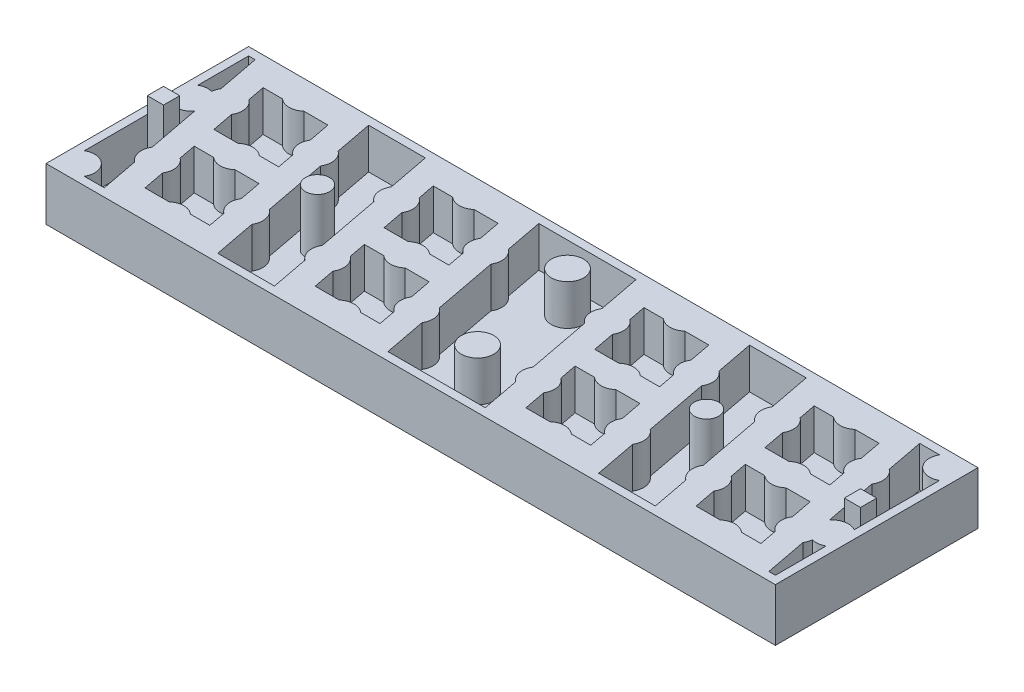
SolidWorks part; units mm, degrees
ref_plane "Спереди" through (0, 0, 0) normal (0, 0, 1) x (1, 0, 0)
ref_plane "Сверху" through (0, 0, 0) normal (0, 1, 0) x (1, 0, 0)
ref_plane "Сбоку" through (0, 0, 0) normal (1, 0, 0) x (0, 0, -1)
sketch "Эскиз1" plane through (0, 0, 0) normal (0, 1, 0) x (1, 0, 0)
  line L1 (0, 0) -> (90, 0)
  line L2 (0, 0) -> (0, 25)
  line L3 (0, 25) -> (90, 25)
  line L4 (90, 0) -> (90, 25)
  dimension "D1" = 90
  dimension "D2" = 25
extrude "Бобышка-Вытянуть1" add sketch "Эскиз1" along normal blind 1.5
sketch "Эскиз3" plane through (0, 1.5, 0) normal (0, 1, 0) x (1, 0, 0)
  line L0 (0, 25) -> (9, 25) construction
  line L1 (90, 25) -> (0, 25) construction
  line L2 (9, 25) -> (30, 25) construction
  line L3 (30, 25) -> (56, 25) construction
  line L4 (56, 25) -> (77, 25) construction
  line L5 (41.1905, 1) -> (53.1905, 1)
  line L6 (37.7143, 3.5) -> (35.3229, 3.5)
  line L7 (20.1905, 1) -> (27.1905, 1)
  line L8 (15.8095, 24) -> (22.8095, 24)
  line L9 (36.8095, 24) -> (48.8095, 24)
  line L10 (58.6771, 3.5) -> (55.7143, 3.5)
  line L11 (23.7995, 18.8027) -> (22.8095, 24)
  line L12 (35.7143, 14) -> (35.3056, 16.1459)
  line L13 (27.1905, 1) -> (26.3056, 5.6459)
  line L14 (2.7995, 18.8027) -> (1.8095, 24)
  line L15 (14.7143, 14) -> (14.3056, 16.1459)
  line L16 (6.1905, 1) -> (5.3056, 5.6459)
  line L17 (4.7995, 8.3027) -> (3.5695, 14.7603)
  line L18 (13.7995, 18.8027) -> (13.2857, 21.5)
  line L19 (20.1905, 1) -> (19.2005, 6.1973)
  line L20 (18.6944, 8.8541) -> (17.2005, 16.6973)
  line L21 (16.6944, 19.3541) -> (15.8095, 24)
  line L22 (25.7995, 8.3027) -> (24.3056, 16.1459)
  line L23 (8.7143, 3.5) -> (8.2005, 6.1973)
  line L24 (7.6944, 8.8541) -> (7.2857, 11)
  line L25 (34.7995, 18.8027) -> (34.2857, 21.5)
  line L26 (16.7143, 3.5) -> (16.3056, 5.6459)
  line L27 (15.7995, 8.3027) -> (15.2857, 11)
  line L28 (15.2857, 11) -> (12.3229, 11)
  line L29 (7.6771, 21.5) -> (5.2857, 21.5)
  line L30 (10.3229, 21.5) -> (13.2857, 21.5)
  line L31 (5.2857, 21.5) -> (5.6944, 19.3541)
  line L32 (14.7143, 14) -> (12.3229, 14)
  line L33 (1, 24) -> (1.8095, 24)
  line L34 (16.7143, 3.5) -> (14.3229, 3.5)
  line L35 (1, 24) -> (1, 17.7321)
  line L36 (3.7321, 1) -> (6.1905, 1)
  line L37 (89, 21.2679) -> (89, 10.7321)
  line L38 (9.6771, 11) -> (7.2857, 11)
  line L39 (9.6771, 14) -> (6.7143, 14)
  line L40 (6.7143, 14) -> (6.2005, 16.6973)
  line L41 (41.1905, 1) -> (40.2005, 6.1973)
  line L42 (39.6944, 8.8541) -> (38.2005, 16.6973)
  line L43 (37.6944, 19.3541) -> (36.8095, 24)
  line L44 (29.7143, 3.5) -> (29.2005, 6.1973)
  line L45 (28.6944, 8.8541) -> (28.2857, 11)
  line L46 (37.7143, 3.5) -> (37.3056, 5.6459)
  line L47 (36.7995, 8.3027) -> (36.2857, 11)
  line L48 (36.2857, 11) -> (33.3229, 11)
  line L49 (28.6771, 21.5) -> (26.2857, 21.5)
  line L50 (31.3229, 21.5) -> (34.2857, 21.5)
  line L51 (26.2857, 21.5) -> (26.6944, 19.3541)
  line L52 (35.7143, 14) -> (33.3229, 14)
  line L53 (63.7143, 3.5) -> (61.3229, 3.5)
  line L54 (30.6771, 11) -> (28.2857, 11)
  line L55 (30.6771, 14) -> (27.7143, 14)
  line L56 (27.7143, 14) -> (27.2005, 16.6973)
  line L57 (62.8095, 24) -> (69.8095, 24)
  line L59 (49.7995, 18.8027) -> (48.8095, 24)
  line L60 (61.7143, 14) -> (61.3056, 16.1459)
  line L61 (53.1905, 1) -> (52.3056, 5.6459)
  line L62 (51.7995, 8.3027) -> (50.3056, 16.1459)
  line L63 (60.7995, 18.8027) -> (60.2857, 21.5)
  line L64 (67.1905, 1) -> (66.2005, 6.1973)
  line L65 (65.6944, 8.8541) -> (64.2005, 16.6973)
  line L66 (63.6944, 19.3541) -> (62.8095, 24)
  line L67 (55.7143, 3.5) -> (55.2005, 6.1973)
  line L68 (54.6944, 8.8541) -> (54.2857, 11)
  line L69 (63.7143, 3.5) -> (63.3056, 5.6459)
  line L70 (62.7995, 8.3027) -> (62.2857, 11)
  line L71 (62.2857, 11) -> (59.3229, 11)
  line L72 (54.6771, 21.5) -> (52.2857, 21.5)
  line L73 (57.3229, 21.5) -> (60.2857, 21.5)
  line L74 (52.2857, 21.5) -> (52.6944, 19.3541)
  line L75 (61.7143, 14) -> (59.3229, 14)
  line L76 (79.6771, 3.5) -> (76.7143, 3.5)
  line L77 (56.6771, 11) -> (54.2857, 11)
  line L78 (56.6771, 14) -> (53.7143, 14)
  line L79 (53.7143, 14) -> (53.2005, 16.6973)
  line L80 (67.1905, 1) -> (74.1905, 1)
  line L81 (84.7143, 3.5) -> (82.3229, 3.5)
  line L82 (70.7995, 18.8027) -> (69.8095, 24)
  line L83 (82.7143, 14) -> (82.3056, 16.1459)
  line L84 (74.1905, 1) -> (73.3056, 5.6459)
  line L85 (72.7995, 8.3027) -> (71.3056, 16.1459)
  line L86 (81.7995, 18.8027) -> (81.2857, 21.5)
  line L87 (88.1905, 1) -> (87.2005, 6.1973)
  line L88 (86.4305, 10.2397) -> (85.2005, 16.6973)
  line L89 (84.6944, 19.3541) -> (83.8095, 24)
  line L90 (76.7143, 3.5) -> (76.2005, 6.1973)
  line L91 (75.6944, 8.8541) -> (75.2857, 11)
  line L92 (84.7143, 3.5) -> (84.3056, 5.6459)
  line L93 (83.7995, 8.3027) -> (83.2857, 11)
  line L94 (83.2857, 11) -> (80.3229, 11)
  line L95 (75.6771, 21.5) -> (73.2857, 21.5)
  line L96 (78.3229, 21.5) -> (81.2857, 21.5)
  line L97 (73.2857, 21.5) -> (73.6944, 19.3541)
  line L98 (82.7143, 14) -> (80.3229, 14)
  line L100 (77.6771, 11) -> (75.2857, 11)
  line L101 (77.6771, 14) -> (74.7143, 14)
  line L102 (74.7143, 14) -> (74.2005, 16.6973)
  line L103 (88.1905, 1) -> (89, 1)
  line L104 (83.8095, 24) -> (86.2679, 24)
  line L105 (1, 14.2679) -> (1, 3.7321)
  line L106 (0, 25) -> (90, 25)
  line L107 (0, 25) -> (0, 0)
  line L108 (0, 0) -> (90, 0)
  line L109 (90, 25) -> (90, 0)
  line L110 (11.6771, 3.5) -> (8.7143, 3.5)
  line L111 (89, 7.2679) -> (89, 1)
  line L113 (32.6771, 3.5) -> (29.7143, 3.5)
  arc A0 (7.6771, 21.5) -> (10.3229, 21.5) centre (9, 23) ccw
  arc A1 (4.7995, 8.3027) -> (5.3056, 5.6459) centre (6.5, 7.25) ccw
  arc A2 (2.7995, 18.8027) -> (2.5085, 17.9343) centre (4.5, 17.75) ccw
  arc A3 (12.3229, 14) -> (9.6771, 14) centre (11, 12.5) ccw
  arc A4 (9.6771, 11) -> (12.3229, 11) centre (11, 12.5) ccw
  arc A5 (8.2005, 6.1973) -> (7.6944, 8.8541) centre (6.5, 7.25) ccw
  arc A6 (6.2005, 16.6973) -> (5.6944, 19.3541) centre (4.5, 17.75) ccw
  arc A7 (17.2005, 16.6973) -> (16.6944, 19.3541) centre (15.5, 17.75) ccw
  arc A8 (14.3229, 3.5) -> (11.6771, 3.5) centre (13, 2) ccw
  arc A9 (13.7995, 18.8027) -> (14.3056, 16.1459) centre (15.5, 17.75) ccw
  arc A10 (19.2005, 6.1973) -> (18.6944, 8.8541) centre (17.5, 7.25) ccw
  arc A11 (28.6771, 21.5) -> (31.3229, 21.5) centre (30, 23) ccw
  arc A12 (15.7995, 8.3027) -> (16.3056, 5.6459) centre (17.5, 7.25) ccw
  arc A13 (25.7995, 8.3027) -> (26.3056, 5.6459) centre (27.5, 7.25) ccw
  arc A14 (23.7995, 18.8027) -> (24.3056, 16.1459) centre (25.5, 17.75) ccw
  arc A15 (33.3229, 14) -> (30.6771, 14) centre (32, 12.5) ccw
  arc A16 (30.6771, 11) -> (33.3229, 11) centre (32, 12.5) ccw
  arc A17 (29.2005, 6.1973) -> (28.6944, 8.8541) centre (27.5, 7.25) ccw
  arc A18 (27.2005, 16.6973) -> (26.6944, 19.3541) centre (25.5, 17.75) ccw
  arc A19 (38.2005, 16.6973) -> (37.6944, 19.3541) centre (36.5, 17.75) ccw
  arc A20 (35.3229, 3.5) -> (32.6771, 3.5) centre (34, 2) ccw
  arc A21 (34.7995, 18.8027) -> (35.3056, 16.1459) centre (36.5, 17.75) ccw
  arc A22 (40.2005, 6.1973) -> (39.6944, 8.8541) centre (38.5, 7.25) ccw
  arc A23 (36.7995, 8.3027) -> (37.3056, 5.6459) centre (38.5, 7.25) ccw
  arc A24 (54.6771, 21.5) -> (57.3229, 21.5) centre (56, 23) ccw
  arc A25 (51.7995, 8.3027) -> (52.3056, 5.6459) centre (53.5, 7.25) ccw
  arc A26 (49.7995, 18.8027) -> (50.3056, 16.1459) centre (51.5, 17.75) ccw
  arc A27 (59.3229, 14) -> (56.6771, 14) centre (58, 12.5) ccw
  arc A28 (56.6771, 11) -> (59.3229, 11) centre (58, 12.5) ccw
  arc A29 (55.2005, 6.1973) -> (54.6944, 8.8541) centre (53.5, 7.25) ccw
  arc A30 (53.2005, 16.6973) -> (52.6944, 19.3541) centre (51.5, 17.75) ccw
  arc A31 (64.2005, 16.6973) -> (63.6944, 19.3541) centre (62.5, 17.75) ccw
  arc A32 (61.3229, 3.5) -> (58.6771, 3.5) centre (60, 2) ccw
  arc A33 (60.7995, 18.8027) -> (61.3056, 16.1459) centre (62.5, 17.75) ccw
  arc A34 (66.2005, 6.1973) -> (65.6944, 8.8541) centre (64.5, 7.25) ccw
  arc A35 (62.7995, 8.3027) -> (63.3056, 5.6459) centre (64.5, 7.25) ccw
  arc A36 (75.6771, 21.5) -> (78.3229, 21.5) centre (77, 23) ccw
  arc A37 (72.7995, 8.3027) -> (73.3056, 5.6459) centre (74.5, 7.25) ccw
  arc A38 (70.7995, 18.8027) -> (71.3056, 16.1459) centre (72.5, 17.75) ccw
  arc A39 (80.3229, 14) -> (77.6771, 14) centre (79, 12.5) ccw
  arc A40 (77.6771, 11) -> (80.3229, 11) centre (79, 12.5) ccw
  arc A41 (76.2005, 6.1973) -> (75.6944, 8.8541) centre (74.5, 7.25) ccw
  arc A42 (74.2005, 16.6973) -> (73.6944, 19.3541) centre (72.5, 17.75) ccw
  arc A43 (85.2005, 16.6973) -> (84.6944, 19.3541) centre (83.5, 17.75) ccw
  arc A44 (82.3229, 3.5) -> (79.6771, 3.5) centre (81, 2) ccw
  arc A45 (81.7995, 18.8027) -> (82.3056, 16.1459) centre (83.5, 17.75) ccw
  arc A46 (87.2005, 6.1973) -> (87.4915, 7.0657) centre (85.5, 7.25) ccw
  arc A47 (83.7995, 8.3027) -> (84.3056, 5.6459) centre (85.5, 7.25) ccw
  arc A48 (3.7321, 1) -> (1, 3.7321) centre (2, 2) ccw
  arc A49 (2.5085, 17.9343) -> (1, 17.7321) centre (2, 16) ccw
  arc A50 (87.4915, 7.0657) -> (89, 7.2679) centre (88, 9) ccw
  arc A51 (86.2679, 24) -> (89, 21.2679) centre (88, 23) ccw
  arc A52 (89, 10.7321) -> (86.4305, 10.2397) centre (88, 9) ccw
  arc A53 (1, 14.2679) -> (3.5695, 14.7603) centre (2, 16) ccw
extrude "Бобышка-Вытянуть2" add sketch "Эскиз3" along normal blind 5
sketch "Эскиз5" plane through (0, 1.5, 0) normal (0, 1, 0) x (1, 0, 0)
  circle A0 centre (43.388, 20.9628) radius 2
extrude "Бобышка-Вытянуть3" add sketch "Эскиз5" along normal blind 5
sketch "Эскиз6" plane through (0, 1.5, 0) normal (0, 1, 0) x (1, 0, 0)
  circle A0 centre (46, 7.25) radius 2
extrude "Бобышка-Вытянуть7" add sketch "Эскиз6" along normal blind 5
sketch "Эскиз7" plane through (0, 0, 0) normal (0, -1, 0) x (1, 0, 0)
  line L0 (5.5126, -13.0576) -> (6.0114, -13.5564)
  line L1 (17.2298, -2.7) -> (8.5035, -2.7)
  line L2 (5.9368, -12.6333) -> (6.7702, -11.8)
  line L3 (5.9368, -12.6333) -> (6.5035, -13.2)
  line L4 (17.4965, -1.3) -> (8.7702, -1.3)
  line L5 (15.9886, -11.4436) -> (17.5543, -3.2241)
  line L6 (4.4457, -21.7759) -> (6.0114, -13.5564)
  line L7 (2.95, -22.1465) -> (4.4856, -14.0846)
  line L8 (6.4457, -11.2759) -> (8.0114, -3.0564)
  line L9 (15.2298, -13.2) -> (6.5035, -13.2)
  line L10 (15.4965, -11.8) -> (6.7702, -11.8)
  line L11 (5.5126, -12.2091) -> (6.4457, -11.2759)
  line L13 (13.4965, -22.3) -> (4.7702, -22.3)
  line L14 (16.0632, -12.3667) -> (15.4965, -11.8)
  line L15 (15.5144, -21.4154) -> (17.05, -13.3535)
  line L16 (13.9886, -21.9436) -> (15.5543, -13.7241)
  line L17 (4.95, -11.6465) -> (6.4856, -3.5846)
  line L18 (16.0632, -12.3667) -> (15.2298, -13.2)
  line L19 (16.4874, -11.9424) -> (15.9886, -11.4436)
  line L20 (4.95, -11.6465) -> (5.5126, -12.2091)
  line L21 (3.9368, -23.1333) -> (4.7702, -22.3)
  line L22 (3.9368, -23.1333) -> (4.5035, -23.7)
  line L23 (4.4856, -14.0846) -> (5.5126, -13.0576)
  line L24 (3.5126, -22.7091) -> (4.4457, -21.7759)
  line L25 (16.4874, -12.7909) -> (15.5543, -13.7241)
  line L26 (2.95, -22.1465) -> (3.5126, -22.7091)
  line L27 (17.5144, -10.9154) -> (19.05, -2.8535)
  line L28 (17.5144, -10.9154) -> (16.4874, -11.9424)
  line L29 (7.5126, -2.5576) -> (8.0114, -3.0564)
  line L30 (7.9368, -2.1333) -> (8.7702, -1.3)
  line L31 (7.9368, -2.1333) -> (8.5035, -2.7)
  line L32 (13.2298, -23.7) -> (4.5035, -23.7)
  line L33 (26.5126, -13.0576) -> (27.0114, -13.5564)
  line L34 (14.0632, -22.8667) -> (13.4965, -22.3)
  line L35 (6.4856, -3.5846) -> (7.5126, -2.5576)
  line L36 (17.05, -13.3535) -> (16.4874, -12.7909)
  line L37 (14.0632, -22.8667) -> (13.2298, -23.7)
  line L38 (14.4874, -22.4424) -> (13.9886, -21.9436)
  line L39 (38.2298, -2.7) -> (29.5035, -2.7)
  line L40 (15.5144, -21.4154) -> (14.4874, -22.4424)
  line L41 (26.9368, -12.6333) -> (27.7702, -11.8)
  line L42 (26.9368, -12.6333) -> (27.5035, -13.2)
  line L43 (38.4965, -1.3) -> (29.7702, -1.3)
  line L44 (18.0632, -1.8667) -> (17.4965, -1.3)
  line L45 (18.0632, -1.8667) -> (17.2298, -2.7)
  line L46 (36.9886, -11.4436) -> (38.5543, -3.2241)
  line L47 (18.4874, -2.2909) -> (17.5543, -3.2241)
  line L48 (25.4457, -21.7759) -> (27.0114, -13.5564)
  line L49 (23.95, -22.1465) -> (25.4856, -14.0846)
  line L50 (27.4457, -11.2759) -> (29.0114, -3.0564)
  line L51 (19.05, -2.8535) -> (18.4874, -2.2909)
  line L52 (36.2298, -13.2) -> (27.5035, -13.2)
  line L53 (36.4965, -11.8) -> (27.7702, -11.8)
  line L54 (26.5126, -12.2091) -> (27.4457, -11.2759)
  line L56 (34.4965, -22.3) -> (25.7702, -22.3)
  line L57 (37.0632, -12.3667) -> (36.4965, -11.8)
  line L58 (36.5144, -21.4154) -> (38.05, -13.3535)
  line L59 (34.9886, -21.9436) -> (36.5543, -13.7241)
  line L60 (25.95, -11.6465) -> (27.4856, -3.5846)
  line L61 (37.0632, -12.3667) -> (36.2298, -13.2)
  line L62 (37.4874, -11.9424) -> (36.9886, -11.4436)
  line L63 (25.95, -11.6465) -> (26.5126, -12.2091)
  line L64 (24.9368, -23.1333) -> (25.7702, -22.3)
  line L65 (24.9368, -23.1333) -> (25.5035, -23.7)
  line L66 (25.4856, -14.0846) -> (26.5126, -13.0576)
  line L67 (24.5126, -22.7091) -> (25.4457, -21.7759)
  line L68 (37.4874, -12.7909) -> (36.5543, -13.7241)
  line L69 (23.95, -22.1465) -> (24.5126, -22.7091)
  line L70 (38.5144, -10.9154) -> (40.05, -2.8535)
  line L71 (38.5144, -10.9154) -> (37.4874, -11.9424)
  line L72 (28.5126, -2.5576) -> (29.0114, -3.0564)
  line L73 (28.9368, -2.1333) -> (29.7702, -1.3)
  line L74 (28.9368, -2.1333) -> (29.5035, -2.7)
  line L75 (34.2298, -23.7) -> (25.5035, -23.7)
  line L76 (35.0632, -22.8667) -> (34.4965, -22.3)
  line L77 (27.4856, -3.5846) -> (28.5126, -2.5576)
  line L78 (38.05, -13.3535) -> (37.4874, -12.7909)
  line L79 (35.0632, -22.8667) -> (34.2298, -23.7)
  line L80 (35.4874, -22.4424) -> (34.9886, -21.9436)
  line L81 (36.5144, -21.4154) -> (35.4874, -22.4424)
  line L82 (39.0632, -1.8667) -> (38.4965, -1.3)
  line L83 (39.0632, -1.8667) -> (38.2298, -2.7)
  line L84 (39.4874, -2.2909) -> (38.5543, -3.2241)
  line L85 (40.05, -2.8535) -> (39.4874, -2.2909)
  line L86 (52.5126, -13.0576) -> (53.0114, -13.5564)
  line L87 (64.2298, -2.7) -> (55.5035, -2.7)
  line L88 (52.9368, -12.6333) -> (53.7702, -11.8)
  line L89 (52.9368, -12.6333) -> (53.5035, -13.2)
  line L90 (64.4965, -1.3) -> (55.7702, -1.3)
  line L91 (62.9886, -11.4436) -> (64.5543, -3.2241)
  line L92 (51.4457, -21.7759) -> (53.0114, -13.5564)
  line L93 (49.95, -22.1465) -> (51.4856, -14.0846)
  line L94 (53.4457, -11.2759) -> (55.0114, -3.0564)
  line L95 (62.2298, -13.2) -> (53.5035, -13.2)
  line L96 (62.4965, -11.8) -> (53.7702, -11.8)
  line L97 (52.5126, -12.2091) -> (53.4457, -11.2759)
  line L99 (60.4965, -22.3) -> (51.7702, -22.3)
  line L100 (63.0632, -12.3667) -> (62.4965, -11.8)
  line L101 (62.5144, -21.4154) -> (64.05, -13.3535)
  line L102 (60.9886, -21.9436) -> (62.5543, -13.7241)
  line L103 (51.95, -11.6465) -> (53.4856, -3.5846)
  line L104 (63.0632, -12.3667) -> (62.2298, -13.2)
  line L105 (63.4874, -11.9424) -> (62.9886, -11.4436)
  line L106 (51.95, -11.6465) -> (52.5126, -12.2091)
  line L107 (50.9368, -23.1333) -> (51.7702, -22.3)
  line L108 (50.9368, -23.1333) -> (51.5035, -23.7)
  line L109 (51.4856, -14.0846) -> (52.5126, -13.0576)
  line L110 (50.5126, -22.7091) -> (51.4457, -21.7759)
  line L111 (63.4874, -12.7909) -> (62.5543, -13.7241)
  line L112 (49.95, -22.1465) -> (50.5126, -22.7091)
  line L113 (64.5144, -10.9154) -> (66.05, -2.8535)
  line L114 (64.5144, -10.9154) -> (63.4874, -11.9424)
  line L115 (54.5126, -2.5576) -> (55.0114, -3.0564)
  line L116 (54.9368, -2.1333) -> (55.7702, -1.3)
  line L117 (54.9368, -2.1333) -> (55.5035, -2.7)
  line L118 (60.2298, -23.7) -> (51.5035, -23.7)
  line L119 (61.0632, -22.8667) -> (60.4965, -22.3)
  line L120 (53.4856, -3.5846) -> (54.5126, -2.5576)
  line L121 (64.05, -13.3535) -> (63.4874, -12.7909)
  line L122 (61.0632, -22.8667) -> (60.2298, -23.7)
  line L123 (61.4874, -22.4424) -> (60.9886, -21.9436)
  line L124 (62.5144, -21.4154) -> (61.4874, -22.4424)
  line L125 (65.0632, -1.8667) -> (64.4965, -1.3)
  line L126 (65.0632, -1.8667) -> (64.2298, -2.7)
  line L127 (65.4874, -2.2909) -> (64.5543, -3.2241)
  line L128 (66.05, -2.8535) -> (65.4874, -2.2909)
  line L129 (73.5126, -13.0576) -> (74.0114, -13.5564)
  line L130 (85.2298, -2.7) -> (76.5035, -2.7)
  line L131 (73.9368, -12.6333) -> (74.7702, -11.8)
  line L132 (73.9368, -12.6333) -> (74.5035, -13.2)
  line L133 (85.4965, -1.3) -> (76.7702, -1.3)
  line L134 (83.9886, -11.4436) -> (85.5543, -3.2241)
  line L135 (72.4457, -21.7759) -> (74.0114, -13.5564)
  line L136 (70.95, -22.1465) -> (72.4856, -14.0846)
  line L137 (74.4457, -11.2759) -> (76.0114, -3.0564)
  line L138 (83.2298, -13.2) -> (74.5035, -13.2)
  line L139 (83.4965, -11.8) -> (74.7702, -11.8)
  line L140 (73.5126, -12.2091) -> (74.4457, -11.2759)
  line L142 (81.4965, -22.3) -> (72.7702, -22.3)
  line L143 (84.0632, -12.3667) -> (83.4965, -11.8)
  line L144 (83.5144, -21.4154) -> (85.05, -13.3535)
  line L145 (81.9886, -21.9436) -> (83.5543, -13.7241)
  line L146 (72.95, -11.6465) -> (74.4856, -3.5846)
  line L147 (84.0632, -12.3667) -> (83.2298, -13.2)
  line L148 (84.4874, -11.9424) -> (83.9886, -11.4436)
  line L149 (72.95, -11.6465) -> (73.5126, -12.2091)
  line L150 (71.9368, -23.1333) -> (72.7702, -22.3)
  line L151 (71.9368, -23.1333) -> (72.5035, -23.7)
  line L152 (72.4856, -14.0846) -> (73.5126, -13.0576)
  line L153 (71.5126, -22.7091) -> (72.4457, -21.7759)
  line L154 (84.4874, -12.7909) -> (83.5543, -13.7241)
  line L155 (70.95, -22.1465) -> (71.5126, -22.7091)
  line L156 (85.5144, -10.9154) -> (87.05, -2.8535)
  line L157 (85.5144, -10.9154) -> (84.4874, -11.9424)
  line L158 (75.5126, -2.5576) -> (76.0114, -3.0564)
  line L159 (75.9368, -2.1333) -> (76.7702, -1.3)
  line L160 (75.9368, -2.1333) -> (76.5035, -2.7)
  line L161 (81.2298, -23.7) -> (72.5035, -23.7)
  line L162 (82.0632, -22.8667) -> (81.4965, -22.3)
  line L163 (74.4856, -3.5846) -> (75.5126, -2.5576)
  line L164 (85.05, -13.3535) -> (84.4874, -12.7909)
  line L165 (82.0632, -22.8667) -> (81.2298, -23.7)
  line L166 (82.4874, -22.4424) -> (81.9886, -21.9436)
  line L167 (83.5144, -21.4154) -> (82.4874, -22.4424)
  line L168 (86.0632, -1.8667) -> (85.4965, -1.3)
  line L169 (86.0632, -1.8667) -> (85.2298, -2.7)
  line L170 (86.4874, -2.2909) -> (85.5543, -3.2241)
  line L171 (87.05, -2.8535) -> (86.4874, -2.2909)
  circle A0 centre (43.388, -20.9628) radius 1.4
  circle A1 centre (46, -7.25) radius 1.4
  circle A2 centre (2, -2) radius 1.4
  circle A3 centre (2, -16) radius 1.4
  circle A4 centre (88, -9) radius 1.4
  circle A5 centre (88, -23) radius 1.4
extrude "Бобышка-Вытянуть8" add sketch "Эскиз7" along normal blind 0.01
sketch "Эскиз9" plane through (0, 1.5, 0) normal (0, 1, 0) x (1, 0, 0)
  line L5 (1, 13.5) -> (3, 13.5)
  line L6 (1, 13.5) -> (1, 11.5)
  line L7 (1, 11.5) -> (3, 11.5)
  line L8 (3, 13.5) -> (3, 11.5)
  line L13 (87, 13.5) -> (87, 11.5)
  line L14 (89, 11.5) -> (87, 11.5)
  line L15 (89, 13.5) -> (89, 11.5)
  line L16 (89, 13.5) -> (87, 13.5)
  circle A0 centre (21, 12.5) radius 1.5
  circle A1 centre (69, 12.5) radius 1.5
extrude "Бобышка-Вытянуть9" add sketch "Эскиз9" along normal blind 7
